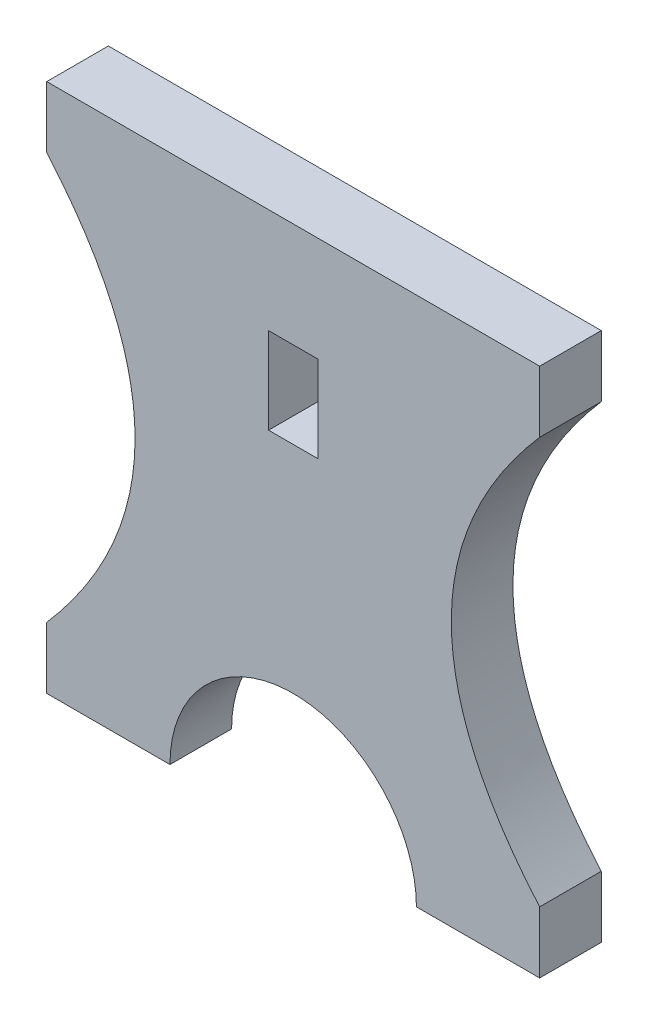
SolidWorks part; units mm, degrees
ref_plane "Спереди" through (0, 0, 0) normal (0, 0, 1) x (1, 0, 0)
ref_plane "Сверху" through (0, 0, 0) normal (0, 1, 0) x (1, 0, 0)
ref_plane "Справа" through (0, 0, 0) normal (1, 0, 0) x (0, 0, -1)
sketch "Эскиз1" plane through (0, 0, 0) normal (0, 0, 1) x (1, 0, 0)
  line L0 (0, 262.3394) -> (0, -266.7981) construction
  line L1 (-206.4251, 0) -> (195.8089, 0) construction
  line L2 (-100, -215) -> (-200, -215)
  line L3 (200, -215) -> (100, -215)
  line L4 (-200, -215) -> (-200, -165)
  line L5 (-200, 215) -> (0, 215)
  line L6 (-200, 215) -> (-200, 165)
  line L7 (200, -215) -> (-200, 215) construction
  line L8 (200, 215) -> (-200, -215) construction
  line L9 (0, 215) -> (200, 215)
  line L10 (-20, 130) -> (20, 130)
  line L11 (-20, 130) -> (-20, 60)
  line L12 (-20, 60) -> (20, 60)
  line L13 (20, 130) -> (20, 60)
  line L14 (-20, 130) -> (20, 60) construction
  line L15 (-20, 60) -> (20, 130) construction
  line L27 (200, 165) -> (200, 215)
  line L30 (200, -215) -> (200, -165)
  arc A0 (100, -215) -> (-100, -215) centre (0, -215) ccw
  spline S0 degree 2 poles (200, 165) (56.658, 0) (200, -165) knots 0 0 0 1 1 1
  spline S1 degree 2 poles (-200, 165) (-56.658, 0) (-200, -165) knots 0 0 0 1 1 1
  point P5 (0, 0)
  point P19 (0, 95)
  dimension "D3" = 100
  dimension "D5" = 215
  dimension "D1" = 430
  dimension "D2" = 400
  dimension "D4" = 50
  dimension "D6" = 40
  dimension "D7" = 70
  dimension "D8" = 60
  dimension "D13" = 50
  dimension "D14" = 100
extrude "Бобышка-Вытянуть3" add sketch "Эскиз1" along normal blind 50
sketch "Эскиз6" plane through (0, 215, 0) normal (0, 1, 0) x (1, 0, 0)
  line L0 (-200, -50) -> (-200, 0) construction
  line L1 (-190, -10) -> (-160, -10)
  line L2 (-190, -10) -> (-190, -40)
  line L3 (-190, -40) -> (-160, -40)
  line L4 (-160, -10) -> (-160, -40)
  line L5 (-190, -10) -> (-160, -40) construction
  line L6 (-190, -40) -> (-160, -10) construction
  line L7 (200, 0) -> (-200, 0) construction
  line L8 (200, -50) -> (200, 0) construction
  line L9 (-140, -10) -> (-110, -10)
  line L10 (-140, -10) -> (-140, -40)
  line L11 (-140, -40) -> (-110, -40)
  line L12 (-110, -10) -> (-110, -40)
  line L13 (-140, -10) -> (-110, -40) construction
  line L14 (-140, -40) -> (-110, -10) construction
  line L16 (-90, -10) -> (-60, -10)
  line L17 (-90, -10) -> (-90, -40)
  line L18 (-90, -40) -> (-60, -40)
  line L19 (-60, -10) -> (-60, -40)
  line L20 (-90, -10) -> (-60, -40) construction
  line L21 (-40, -10) -> (-10, -10)
  line L22 (-40, -10) -> (-40, -40)
  line L23 (-40, -40) -> (-10, -40)
  line L24 (-10, -10) -> (-10, -40)
  line L25 (-40, -10) -> (-10, -40) construction
  line L26 (-40, -40) -> (-10, -10) construction
  line L27 (10, -10) -> (40, -10)
  line L28 (10, -10) -> (10, -40)
  line L29 (10, -40) -> (40, -40)
  line L30 (40, -10) -> (40, -40)
  line L31 (10, -10) -> (40, -40) construction
  line L32 (10, -40) -> (40, -10) construction
  line L33 (60, -10) -> (90, -10)
  line L34 (60, -10) -> (60, -40)
  line L35 (60, -40) -> (90, -40)
  line L36 (90, -10) -> (90, -40)
  line L37 (60, -10) -> (90, -40) construction
  line L38 (60, -40) -> (90, -10) construction
  line L39 (110, -10) -> (140, -10)
  line L40 (110, -10) -> (110, -40)
  line L41 (110, -40) -> (140, -40)
  line L42 (140, -10) -> (140, -40)
  line L43 (110, -10) -> (140, -40) construction
  line L44 (110, -40) -> (140, -10) construction
  line L45 (160, -10) -> (190, -10)
  line L46 (160, -10) -> (160, -40)
  line L47 (160, -40) -> (190, -40)
  line L48 (190, -10) -> (190, -40)
  line L49 (160, -10) -> (190, -40) construction
  line L50 (160, -40) -> (190, -10) construction
  line L51 (200, -50) -> (-200, -50) construction
  line L52 (-90, -40) -> (-60, -10) construction
  point P0 (-175, -25)
  point P5 (-200, -25)
  point P10 (-125, -25)
  point P15 (-80.2103, -19.7897)
  point P16 (-75, -25)
  point P20 (-25, -25)
  point P25 (25, -25)
  point P30 (75, -25)
  point P35 (125, -25)
  point P40 (175, -25)
  dimension "D1" = 30
  dimension "D2" = 30
  dimension "D3" = 10
  dimension "D4" = 10
  dimension "D5" = 30
  dimension "D6" = 30
  dimension "D7" = 20
  dimension "D8" = 30
  dimension "D9" = 10
  dimension "D10" = 30
  dimension "D11" = 30
  dimension "D12" = 10
  dimension "D13" = 20
  dimension "D14" = 10
  dimension "D15" = 10
  dimension "D16" = 20
  dimension "D17" = 30
  dimension "D18" = 10
  dimension "D19" = 10
  dimension "D20" = 20
  dimension "D21" = 30
  dimension "D22" = 10
  dimension "D23" = 10
  dimension "D24" = 20
  dimension "D25" = 30
  dimension "D26" = 10
  dimension "D27" = 10
  dimension "D28" = 30
  dimension "D29" = 10
  dimension "D30" = 20
